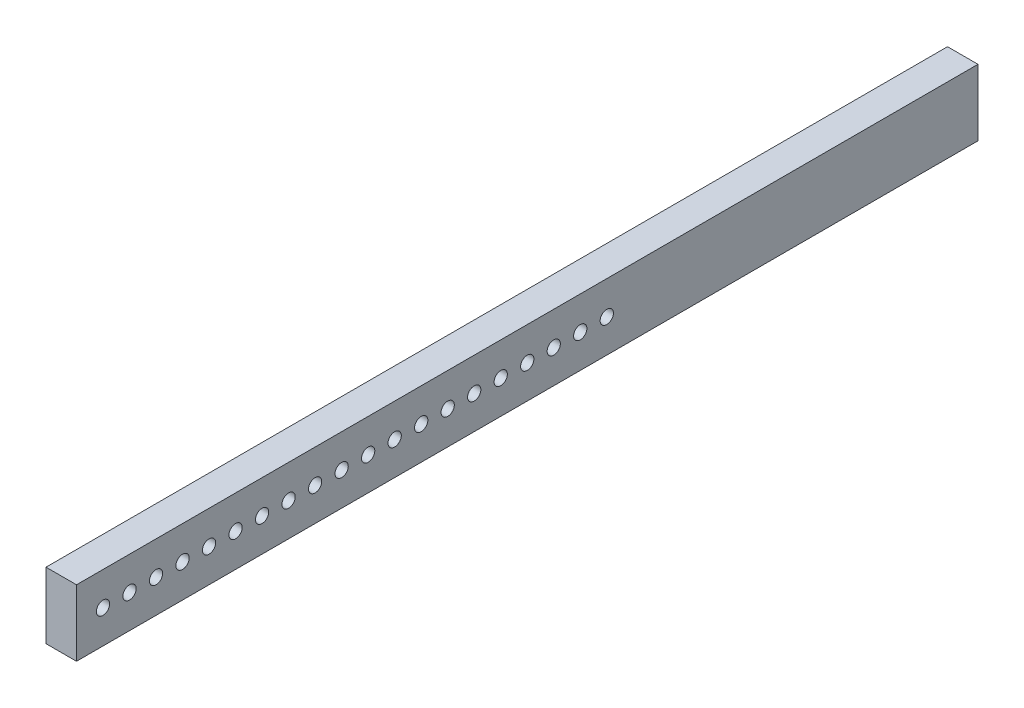
SolidWorks part; units mm, degrees
ref_plane "Front Plane" through (0, 0, 0) normal (0, 0, 1) x (1, 0, 0)
ref_plane "Top Plane" through (0, 0, 0) normal (0, 1, 0) x (1, 0, 0)
ref_plane "Right Plane" through (0, 0, 0) normal (1, 0, 0) x (0, 0, -1)
sketch "Sketch1" plane through (0, 0, 0) normal (1, 0, 0) x (0, 0, -1)
  line L0 (357.9806, 0) -> (-380.156, 0) construction
  line L1 (-340, 25) -> (340, 25)
  line L2 (-340, 25) -> (-340, -25)
  line L3 (-340, -25) -> (340, -25)
  line L4 (340, 25) -> (340, -25)
  line L5 (-340, 25) -> (340, -25) construction
  line L6 (-340, -25) -> (340, 25) construction
  circle A0 centre (-320, 0) radius 5
  circle A1 centre (-300, 0) radius 5
  circle A2 centre (-280, 0) radius 5
  circle A3 centre (-260, 0) radius 5
  circle A4 centre (-240, 0) radius 5
  circle A5 centre (-220, 0) radius 5
  circle A6 centre (-200, 0) radius 5
  circle A7 centre (-180, 0) radius 5
  circle A8 centre (-160, 0) radius 5
  circle A9 centre (-140, 0) radius 5
  circle A10 centre (-120, 0) radius 5
  circle A11 centre (-100, 0) radius 5
  circle A12 centre (-80, 0) radius 5
  circle A13 centre (-60, 0) radius 5
  circle A14 centre (-40, 0) radius 5
  circle A15 centre (-20, 0) radius 5
  circle A16 centre (0, 0) radius 5
  circle A17 centre (20, 0) radius 5
  circle A18 centre (40, 0) radius 5
  circle A19 centre (60, 0) radius 5
  point P0 (0, 0)
  dimension "D3" = 10
  dimension "D1" = 680
  dimension "D2" = 50
  dimension "D4" = 20
extrude "Boss-Extrude1" add sketch "Sketch1" along normal blind 23
